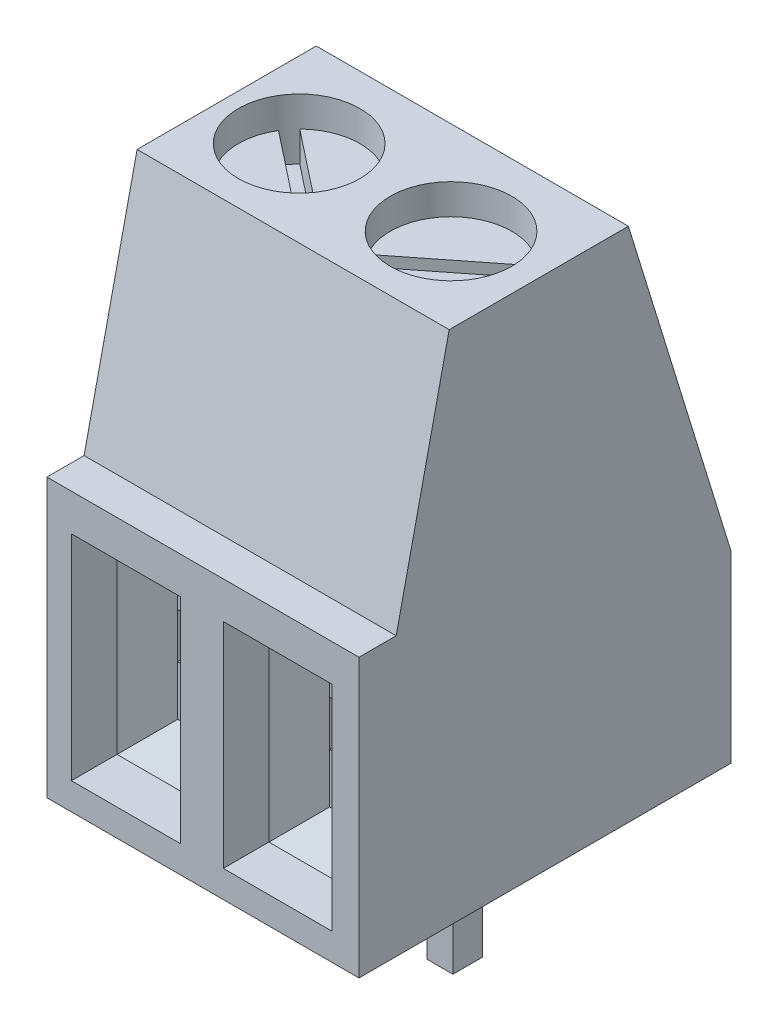
SolidWorks part; units mm, degrees
ref_plane "Front Plane" through (0, 0, 0) normal (0, 0, 1) x (1, 0, 0)
ref_plane "Top Plane" through (0, 0, 0) normal (0, 1, 0) x (1, 0, 0)
ref_plane "Right Plane" through (0, 0, 0) normal (1, 0, 0) x (0, 0, -1)
sketch "Sketch1" plane through (0, 0, 0) normal (0, 1, 0) x (1, 0, 0)
  line L1 (0, 0) -> (20.701, 0)
  line L2 (0, 0) -> (0, 6.223)
  line L3 (0, 6.223) -> (20.701, 6.223)
  line L4 (20.701, 0) -> (20.701, 6.223)
  dimension "D1" = 20.701
  dimension "D2" = 6.223
extrude "Extrude1" add sketch "Sketch1" along normal blind 8.636
sketch "Sketch2" plane through (20.701, 0, 0) normal (1, 0, 0) x (0, 0, -1)
  line L0 (-2.8691, 4.6459) -> (0.6218, 4.6459)
  line L1 (0.6218, 4.6459) -> (2.2176, 11.8272)
  line L2 (2.2176, 11.8272) -> (-2.8691, 11.8272)
  line L3 (-2.8691, 11.8272) -> (-2.8691, 4.6459)
extrude "Cut-Extrude1" cut sketch "Sketch2" against normal blind 25.4
sketch "Sketch3" plane through (20.701, 0, 0) normal (1, 0, 0) x (0, 0, -1)
  line L0 (4.013, 10.2314) -> (6.9054, 0.8558)
  line L1 (6.9054, 0.8558) -> (9.1994, 0.8558)
  line L2 (9.1994, 0.8558) -> (9.1994, 10.2314)
  line L3 (9.1994, 10.2314) -> (4.013, 10.2314)
extrude "Cut-Extrude2" cut sketch "Sketch3" against normal blind 25.4
sketch "Sketch4" plane through (0, 8.636, 0) normal (0, 1, 0) x (1, 0, 0)
  line L0 (0, 4.5051) -> (0, 1.5085) construction
  circle A0 centre (1.27, 2.9491) radius 1.016
  circle A1 centre (3.81, 2.9491) radius 1.016
  circle A2 centre (6.35, 2.9491) radius 1.016
  circle A3 centre (8.89, 2.9491) radius 1.016
  circle A4 centre (11.43, 2.9491) radius 1.016
  circle A5 centre (13.97, 2.9491) radius 1.016
  circle A6 centre (16.51, 2.9491) radius 1.016
  circle A7 centre (19.05, 2.9491) radius 1.016
  dimension "D1" = 1.27
extrude "Cut-Extrude3" cut sketch "Sketch4" against normal blind 0.508
sketch "Sketch5" plane through (0, 8.128, 0) normal (0, 1, 0) x (1, 0, 0)
  line L8 (18.1734, 3.4782) -> (19.7694, 2.2205)
  line L9 (16.7061, 3.9541) -> (16.0726, 2.0233)
  line L10 (12.9692, 3.1653) -> (14.8868, 2.4932)
  line L11 (11.303, 3.9651) -> (11.303, 1.9331)
  line L12 (8.6939, 1.9441) -> (9.3274, 3.8749)
  line L13 (5.334, 2.8221) -> (7.366, 2.8221)
  line L14 (3.0906, 2.2205) -> (4.6866, 3.4782)
  line L15 (0.3934, 3.4782) -> (1.9894, 2.2205)
  line L16 (18.3306, 3.6777) -> (19.9266, 2.42)
  line L17 (16.9474, 3.8749) -> (16.3139, 1.9441)
  line L18 (13.0532, 3.405) -> (14.9708, 2.7329)
  line L19 (11.557, 3.9651) -> (11.557, 1.9331)
  line L20 (8.4526, 2.0233) -> (9.0861, 3.9541)
  line L21 (5.334, 3.0761) -> (7.366, 3.0761)
  line L22 (2.9334, 2.42) -> (4.5294, 3.6777)
  line L23 (0.5506, 3.6777) -> (2.1466, 2.42)
  circle A13 centre (1.27, 2.9491) radius 1.016
  circle A14 centre (3.81, 2.9491) radius 1.016
  circle A15 centre (6.35, 2.9491) radius 1.016
  circle A16 centre (8.89, 2.9491) radius 1.005
  circle A17 centre (11.43, 2.9491) radius 1.016
  circle A18 centre (13.97, 2.9491) radius 1.016
  circle A19 centre (16.51, 2.9491) radius 1.016
  circle A20 centre (19.05, 2.9491) radius 0.9996
  circle M1 centre (1.27, 2.9491) radius 1.016
extrude "Cut-Extrude4" cut sketch "Sketch5" against normal blind 0.508 contours L23 L15 M1 | L14 A14 L22 | L13 A15 L21 | L12 A16 L20 | L19 A17 L11 | L10 A18 L18 | L17 A19 L9 | L8 A20 L16
sketch "Sketch6" plane through (0, 0, 0) normal (0, 0, 1) x (1, 0, 0)
  line L0 (2.9501, 4.0288) -> (2.9501, 0.4524)
  line L1 (0.4101, 4.0288) -> (2.232, 4.0288)
  line L2 (0.4101, 4.0288) -> (0.4101, 0.4524)
  line L3 (0.4101, 0.4524) -> (2.232, 0.4524)
  line L4 (2.232, 4.0288) -> (2.232, 0.4524)
  line L5 (2.9501, 4.0288) -> (4.772, 4.0288)
  line L6 (4.772, 4.0288) -> (4.772, 0.4524)
  line L7 (2.9501, 0.4524) -> (4.772, 0.4524)
  line L8 (5.4901, 4.0288) -> (5.4901, 0.4524)
  line L9 (5.4901, 4.0288) -> (7.312, 4.0288)
  line L10 (7.312, 4.0288) -> (7.312, 0.4524)
  line L11 (5.4901, 0.4524) -> (7.312, 0.4524)
  line L12 (8.0301, 4.0288) -> (8.0301, 0.4524)
  line L13 (8.0301, 4.0288) -> (9.852, 4.0288)
  line L14 (9.852, 4.0288) -> (9.852, 0.4524)
  line L15 (8.0301, 0.4524) -> (9.852, 0.4524)
  line L16 (10.5701, 4.0288) -> (10.5701, 0.4524)
  line L17 (10.5701, 4.0288) -> (12.392, 4.0288)
  line L18 (12.392, 4.0288) -> (12.392, 0.4524)
  line L19 (10.5701, 0.4524) -> (12.392, 0.4524)
  line L20 (13.1101, 4.0288) -> (13.1101, 0.4524)
  line L21 (13.1101, 4.0288) -> (14.932, 4.0288)
  line L22 (14.932, 4.0288) -> (14.932, 0.4524)
  line L23 (13.1101, 0.4524) -> (14.932, 0.4524)
  line L24 (15.6501, 4.0288) -> (15.6501, 0.4524)
  line L25 (15.6501, 4.0288) -> (17.472, 4.0288)
  line L26 (17.472, 4.0288) -> (17.472, 0.4524)
  line L27 (15.6501, 0.4524) -> (17.472, 0.4524)
  line L28 (18.1901, 4.0288) -> (18.1901, 0.4524)
  line L29 (18.1901, 4.0288) -> (20.012, 4.0288)
  line L30 (20.012, 4.0288) -> (20.012, 0.4524)
  line L31 (18.1901, 0.4524) -> (20.012, 0.4524)
extrude "Cut-Extrude5" cut sketch "Sketch6" against normal blind 1.27
chamfer "Chamfer1" distance 0.508 angle 45 7 edges at (4.772, 2.2406, -1.27) (2.9501, 2.2406, -1.27) (3.8611, 4.0288, -1.27) (1.3211, 4.0288, -1.27) (2.232, 2.2406, -1.27) (1.3211, 0.4524, -1.27) (0.4101, 2.2406, -1.27)
sketch "Sketch7" plane through (0, 0, -1.27) normal (0, 0, 1) x (1, 0, 0)
  line L0 (0.9181, 3.5208) -> (0.9181, 0.9604) construction
  line L1 (0.9181, 2.5517) -> (1.724, 2.5517)
  line L2 (0.9181, 2.5517) -> (0.9181, 1.7937)
  line L3 (0.9181, 1.7937) -> (1.724, 1.7937)
  line L4 (1.724, 2.5517) -> (1.724, 1.7937)
  line L5 (1.724, 0.9604) -> (1.724, 3.5208) construction
  line L6 (3.4581, 2.5517) -> (3.4581, 1.7937)
  line L7 (3.4581, 2.5517) -> (4.264, 2.5517)
  line L8 (4.264, 2.5517) -> (4.264, 1.7937)
  line L9 (3.4581, 1.7937) -> (4.264, 1.7937)
  line L10 (5.9981, 2.5517) -> (5.9981, 1.7937)
  line L11 (5.9981, 2.5517) -> (6.804, 2.5517)
  line L12 (6.804, 2.5517) -> (6.804, 1.7937)
  line L13 (5.9981, 1.7937) -> (6.804, 1.7937)
  line L14 (8.5381, 2.5517) -> (8.5381, 1.7937)
  line L15 (8.5381, 2.5517) -> (9.344, 2.5517)
  line L16 (9.344, 2.5517) -> (9.344, 1.7937)
  line L17 (8.5381, 1.7937) -> (9.344, 1.7937)
  line L18 (11.0781, 2.5517) -> (11.0781, 1.7937)
  line L19 (11.0781, 2.5517) -> (11.884, 2.5517)
  line L20 (11.884, 2.5517) -> (11.884, 1.7937)
  line L21 (11.0781, 1.7937) -> (11.884, 1.7937)
  line L22 (13.6181, 2.5517) -> (13.6181, 1.7937)
  line L23 (13.6181, 2.5517) -> (14.424, 2.5517)
  line L24 (14.424, 2.5517) -> (14.424, 1.7937)
  line L25 (13.6181, 1.7937) -> (14.424, 1.7937)
  line L26 (16.1581, 2.5517) -> (16.1581, 1.7937)
  line L27 (16.1581, 2.5517) -> (16.964, 2.5517)
  line L28 (16.964, 2.5517) -> (16.964, 1.7937)
  line L29 (16.1581, 1.7937) -> (16.964, 1.7937)
  line L30 (18.6981, 2.5517) -> (18.6981, 1.7937)
  line L31 (18.6981, 2.5517) -> (19.504, 2.5517)
  line L32 (19.504, 2.5517) -> (19.504, 1.7937)
  line L33 (18.6981, 1.7937) -> (19.504, 1.7937)
extrude "Cut-Extrude6" cut sketch "Sketch7" against normal blind 1.27
sketch "Sketch8" plane through (0, 0, 0) normal (0, -1, 0) x (1, 0, 0)
  line L0 (3.6128, -2.7447) -> (3.6128, -3.2358)
  line L1 (1.0728, -2.7447) -> (1.5062, -2.7447)
  line L2 (1.0728, -2.7447) -> (1.0728, -3.2358)
  line L3 (1.0728, -3.2358) -> (1.5062, -3.2358)
  line L4 (1.5062, -2.7447) -> (1.5062, -3.2358)
  line L5 (3.6128, -2.7447) -> (4.0462, -2.7447)
  line L6 (4.0462, -2.7447) -> (4.0462, -3.2358)
  line L7 (3.6128, -3.2358) -> (4.0462, -3.2358)
  line L8 (6.1528, -2.7447) -> (6.1528, -3.2358)
  line L9 (6.1528, -2.7447) -> (6.5862, -2.7447)
  line L10 (6.5862, -2.7447) -> (6.5862, -3.2358)
  line L11 (6.1528, -3.2358) -> (6.5862, -3.2358)
  line L12 (8.6928, -2.7447) -> (8.6928, -3.2358)
  line L13 (8.6928, -2.7447) -> (9.1262, -2.7447)
  line L14 (9.1262, -2.7447) -> (9.1262, -3.2358)
  line L15 (8.6928, -3.2358) -> (9.1262, -3.2358)
  line L16 (11.2328, -2.7447) -> (11.2328, -3.2358)
  line L17 (11.2328, -2.7447) -> (11.6662, -2.7447)
  line L18 (11.6662, -2.7447) -> (11.6662, -3.2358)
  line L19 (11.2328, -3.2358) -> (11.6662, -3.2358)
  line L20 (13.7728, -2.7447) -> (13.7728, -3.2358)
  line L21 (13.7728, -2.7447) -> (14.2062, -2.7447)
  line L22 (14.2062, -2.7447) -> (14.2062, -3.2358)
  line L23 (13.7728, -3.2358) -> (14.2062, -3.2358)
  line L24 (16.3128, -2.7447) -> (16.3128, -3.2358)
  line L25 (16.3128, -2.7447) -> (16.7462, -2.7447)
  line L26 (16.7462, -2.7447) -> (16.7462, -3.2358)
  line L27 (16.3128, -3.2358) -> (16.7462, -3.2358)
  line L28 (18.8528, -2.7447) -> (18.8528, -3.2358)
  line L29 (18.8528, -2.7447) -> (19.2862, -2.7447)
  line L30 (19.2862, -2.7447) -> (19.2862, -3.2358)
  line L31 (18.8528, -3.2358) -> (19.2862, -3.2358)
extrude "Extrude2" add sketch "Sketch8" along normal blind 1.905
sketch "Sketch9" plane through (0, 8.636, 0) normal (0, 1, 0) x (1, 0, 0)
  line L1 (7.5567, 8.0072) -> (21.3925, 8.0072)
  line L2 (7.5567, 8.0072) -> (7.5567, -3.0614)
  line L3 (7.5567, -3.0614) -> (21.3925, -3.0614)
  line L4 (21.3925, 8.0072) -> (21.3925, -3.0614)
extrude "Cut-Extrude7" cut sketch "Sketch9" against normal blind 25.4
sketch "Sketch10" plane through (0, 8.636, 0) normal (0, 1, 0) x (1, 0, 0)
  line L0 (7.5567, 4.5051) -> (7.5567, 1.5085) construction
  line L1 (5.2199, 8.3689) -> (8.6085, 8.3689)
  line L2 (5.2199, 8.3689) -> (5.2199, -2.1459)
  line L3 (5.2199, -2.1459) -> (8.6085, -2.1459)
  line L4 (8.6085, 8.3689) -> (8.6085, -2.1459)
  dimension "D1" = 2.3368
extrude "Cut-Extrude8" cut sketch "Sketch10" against normal blind 25.4
